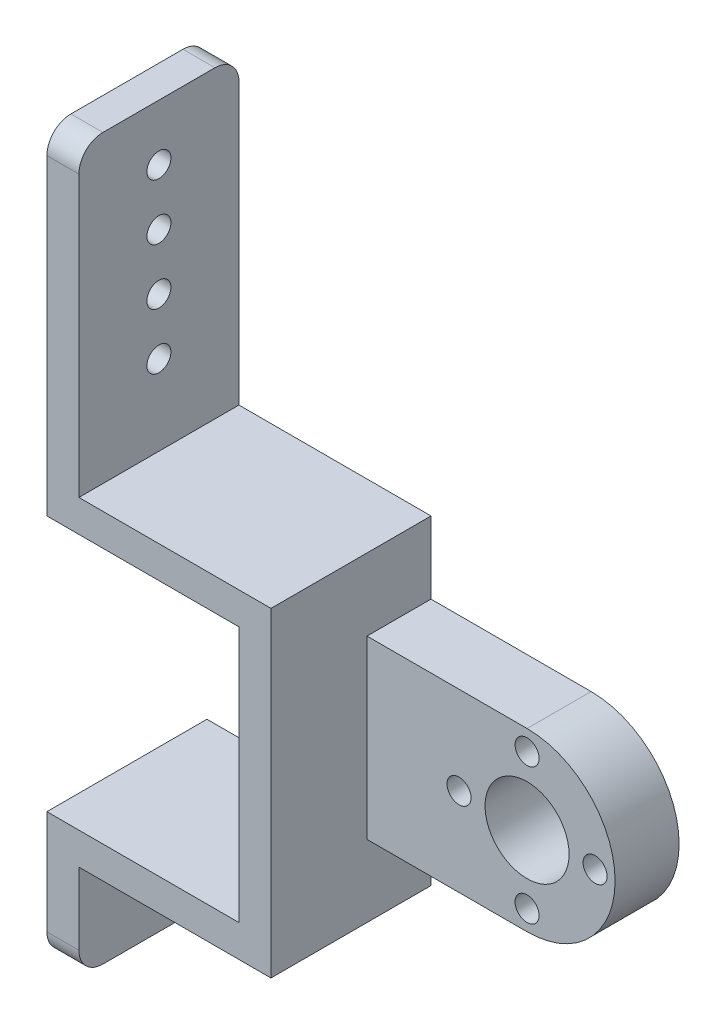
SolidWorks part; units mm, degrees
ref_plane "Front Plane" through (0, 0, 0) normal (0, 0, 1) x (1, 0, 0)
ref_plane "Top Plane" through (0, 0, 0) normal (0, 1, 0) x (1, 0, 0)
ref_plane "Right Plane" through (0, 0, 0) normal (1, 0, 0) x (0, 0, -1)
sketch "Sketch1" plane through (0, 0, 0) normal (0, 0, 1) x (1, 0, 0)
  line L1 (-12, -11) -> (12, -11)
  line L2 (-12, -11) -> (-12, 11)
  line L3 (-12, 11) -> (12, 11)
  line L4 (12, -11) -> (12, 11)
  line L5 (-12, -11) -> (12, 11) construction
  line L6 (-12, 11) -> (12, -11) construction
  circle A0 centre (12, 0) radius 11
  point P0 (0, 0)
  dimension "D1" = 24
  dimension "D2" = 22
extrude "Boss-Extrude2" add sketch "Sketch1" along normal blind 8 contours L4 A0 | L4 A0 | A0 L3 L2 L1
sketch "Sketch3" plane through (0, 0, 8) normal (0, 0, 1) x (1, 0, 0)
  circle A0 centre (12, 0) radius 5.25
  dimension "D1" = 10.5
extrude "Cut-Extrude1" cut sketch "Sketch3" against normal blind 8
sketch "Sketch7" plane through (0, 0, 8) normal (0, 0, 1) x (1, 0, 0)
  line L0 (-12, 11) -> (-12, 20)
  line L1 (-12, 20) -> (-8, 20)
  line L2 (-8, 20) -> (-8, 11)
  line L3 (-12, 11) -> (12, 11) construction
  line L4 (-8, 11) -> (-12, 11)
  line L5 (-12, -11) -> (-12, -20)
  line L6 (-12, -20) -> (-8, -20)
  line L7 (-8, -20) -> (-8, -11)
  line L8 (-12, -11) -> (12, -11) construction
  line L9 (-8, -11) -> (-12, -11)
  dimension "D1" = 9
  dimension "D2" = 4
  dimension "D3" = 9
  dimension "D4" = 4
extrude "Boss-Extrude3" add sketch "Sketch7" against normal blind 8
sketch "Sketch8" plane through (0, 0, 0) normal (0, 0, -1) x (-1, 0, 0)
  line L1 (8, 20) -> (12, 20)
  line L2 (8, 20) -> (8, -20)
  line L3 (8, -20) -> (12, -20)
  line L4 (12, 20) -> (12, -20)
extrude "Boss-Extrude4" add sketch "Sketch8" along normal blind 12
sketch "Sketch9" plane through (-12, 0, 0) normal (-1, 0, 0) x (0, 0, 1)
  line L0 (8, -20) -> (8, 20) construction
  line L1 (-12, 20) -> (8, 20)
  line L2 (-12, 20) -> (-12, 16)
  line L3 (-12, 16) -> (8, 16)
  line L4 (8, 20) -> (8, 16)
  dimension "D1" = 4
extrude "Boss-Extrude5" add sketch "Sketch9" along normal blind 24
sketch "Sketch10" plane through (-12, 0, 0) normal (-1, 0, 0) x (0, 0, 1)
  line L0 (8, -20) -> (8, 16) construction
  line L1 (-12, -20) -> (8, -20)
  line L2 (-12, -20) -> (-12, -16)
  line L3 (-12, -16) -> (8, -16)
  line L4 (8, -20) -> (8, -16)
  dimension "D1" = 4
extrude "Boss-Extrude6" add sketch "Sketch10" along normal blind 24
sketch "Sketch12" plane through (0, 0, -12) normal (0, 0, -1) x (-1, 0, 0)
  line L0 (36, -20) -> (36, 58) construction
  line L2 (36, 20) -> (32, 20)
  line L3 (36, 20) -> (36, 58)
  line L4 (36, 58) -> (32, 58)
  line L5 (32, 20) -> (32, 58)
  dimension "D1" = 78
  dimension "D2" = 4
extrude "Boss-Extrude7" add sketch "Sketch12" against normal blind 20
sketch "Sketch13" plane through (0, -20, 0) normal (0, -1, 0) x (1, 0, 0)
  line L0 (-8, -12) -> (-36, -12) construction
  line L1 (-36, 8) -> (-32, 8)
  line L2 (-36, 8) -> (-36, -12)
  line L3 (-36, -12) -> (-32, -12)
  line L4 (-32, 8) -> (-32, -12)
  dimension "D1" = 4
extrude "Boss-Extrude8" add sketch "Sketch13" along normal blind 12
sketch "Sketch14" plane through (-36, 0, 0) normal (-1, 0, 0) x (0, 0, 1)
  line L0 (8, 58) -> (-12, 58) construction
  circle A0 centre (-2, -27.5) radius 1.5
  dimension "D1" = 3
  dimension "D2" = 85.5
extrude "Cut-Extrude2" cut sketch "Sketch14" against normal blind 12
sketch "Sketch15" plane through (-36, 0, 0) normal (-1, 0, 0) x (0, 0, 1)
  line L0 (8, 58) -> (-12, 58) construction
  circle A0 centre (-2, 51) radius 1.5
  circle A1 centre (-2, 44) radius 1.5
  circle A2 centre (-2, 37) radius 1.5
  circle A3 centre (-2, 30) radius 1.5
  dimension "D1" = 3
  dimension "D2" = 3
  dimension "D3" = 3
  dimension "D4" = 3
  dimension "D5" = 7
  dimension "D6" = 7
  dimension "D7" = 7
  dimension "D8" = 7
extrude "Cut-Extrude3" cut sketch "Sketch15" against normal blind 12
fillet "Fillet1" radius 3 4 edges at (-34, 58, -12) (-34, 58, 8) (-34, -32, -12) (-34, -32, 8)
sketch "Sketch16" plane through (0, 0, 0) normal (0, 0, -1) x (-1, 0, 0)
  line L0 (-12, 5.25) -> (-12, 8.5) construction
  circle A0 centre (-12, 0) radius 5.25 construction
  circle A1 centre (-12, 8.5) radius 1.5
  circle A2 centre (-20.5, 0) radius 1.5
  circle A3 centre (-12, -8.5) radius 1.5
  circle A4 centre (-3.5, 0) radius 1.5
  dimension "D2" = 3
  dimension "D1" = 8.5
  dimension "D3" = 3
  dimension "D4" = 3
  dimension "D5" = 3
  dimension "D6" = 8.5
  dimension "D7" = 8.5
  dimension "D8" = 8.5
extrude "Cut-Extrude4" cut sketch "Sketch16" against normal blind 12
sketch "Sketch21" plane through (-8, 0, 0) normal (1, 0, 0) x (0, 0, -1)
  line L0 (12, 20) -> (12, -20) construction
  line L1 (12, 11) -> (4, 11)
  line L2 (12, 11) -> (12, -11)
  line L3 (12, -11) -> (4, -11)
  line L4 (4, 11) -> (4, -11)
  dimension "D1" = 8
extrude "Boss-Extrude9" add sketch "Sketch21" along normal blind 20
sketch "Sketch22" plane through (0, 0, -12) normal (0, 0, -1) x (-1, 0, 0)
  line L0 (-12, -11) -> (-12, 11) construction
  circle A0 centre (-12, 0) radius 11
extrude "Boss-Extrude10" add sketch "Sketch22" against normal blind 8
sketch "Sketch23" plane through (0, 0, 8) normal (0, 0, 1) x (1, 0, 0)
  circle A0 centre (12, 8.5) radius 1.5
  circle A1 centre (20.5, 0) radius 1.5
  circle A2 centre (3.5, 0) radius 1.5
  circle A3 centre (12, -8.5) radius 1.5
  circle A4 centre (12, 0) radius 5.25
extrude "Cut-Extrude6" cut sketch "Sketch23" against normal through all
sketch "Sketch24" plane through (0, 0, 8) normal (0, 0, 1) x (1, 0, 0)
  line L1 (-8, 11) -> (12, 11)
  line L2 (-8, 11) -> (-8, -11)
  line L3 (-8, -11) -> (12, -11)
  line L4 (12, 11) -> (12, -11)
  circle A0 centre (12, 0) radius 11
  circle M1 centre (12, 8.5) radius 1.5
  circle M2 centre (20.5, 0) radius 1.5
  circle M3 centre (12, -8.5) radius 1.5
  circle M4 centre (3.5, 0) radius 1.5
  circle M5 centre (12, 0) radius 5.25
  line M17 (-8, -11) -> (12, -11)
  arc M18 (12, -11) -> (12, 11) centre (12, 0) ccw
  line M19 (12, 11) -> (-8, 11)
extrude "Cut-Extrude7" cut sketch "Sketch24" against normal blind 8 contours A0 L2 M19 M17 | L4 A0 M3 M5 M1 M4 | L4 M18 M1 M5 M3 M2
